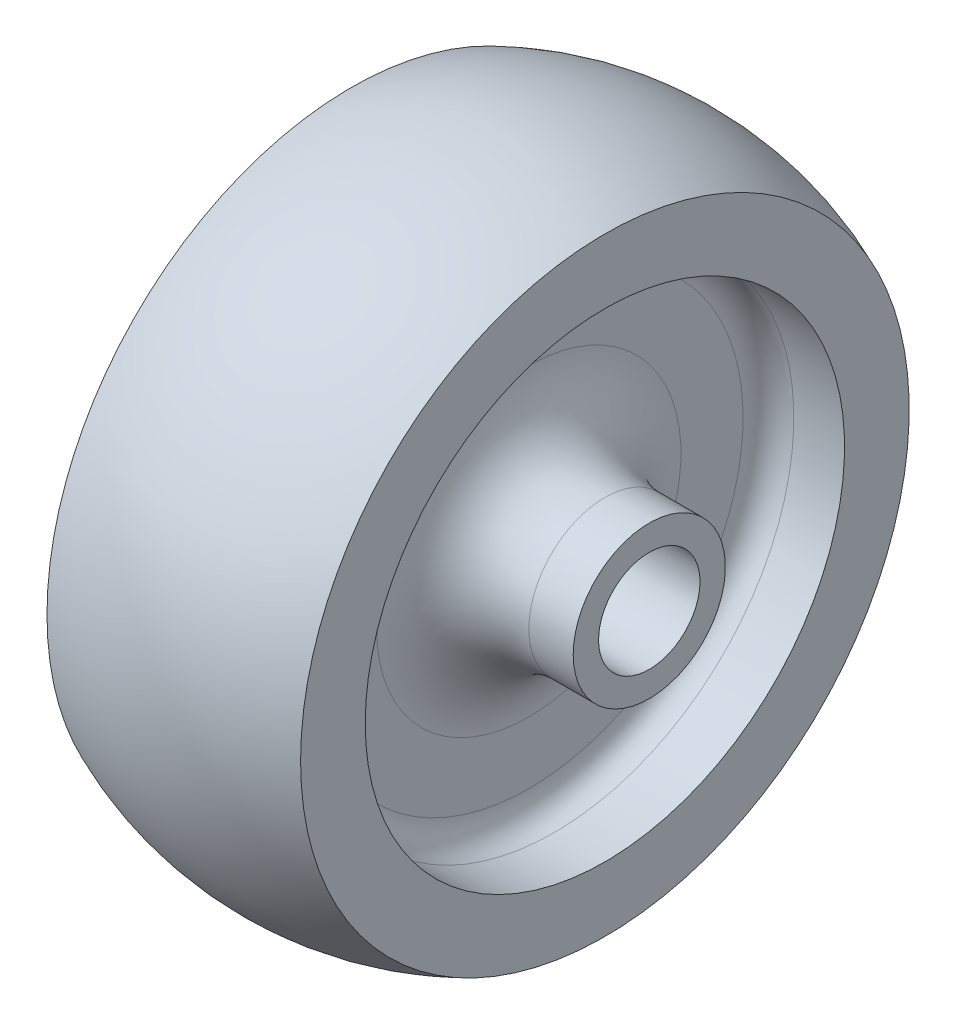
SolidWorks part; units mm, degrees
ref_plane "Front Plane" through (0, 0, 0) normal (0, 0, 1) x (1, 0, 0)
ref_plane "Top Plane" through (0, 0, 0) normal (0, 1, 0) x (1, 0, 0)
ref_plane "Right Plane" through (0, 0, 0) normal (1, 0, 0) x (0, 0, -1)
sketch "Sketch1" plane through (0, 0, 0) normal (0, 0, 1) x (1, 0, 0)
  line L0 (0, 0) -> (21.0336, 0) construction
  line L1 (0, 4) -> (0, 6)
  line L4 (0, 4) -> (27, 4)
  line L6 (0, 6) -> (3.5, 6)
  line L7 (3.5, 18.9) -> (3.5, 24)
  line L8 (23.5, 24) -> (23.5, 18.9)
  line L9 (23.5, 6) -> (27, 6)
  line L10 (27, 6) -> (27, 4)
  line L12 (3.5, 6) -> (9.5, 6)
  line L14 (3.5, 18.9) -> (7.5, 18.9)
  line L15 (9.5, 6) -> (9.5, 16.9)
  line L16 (23.5, 6) -> (17.5, 6)
  line L18 (23.5, 18.9) -> (19.5, 18.9)
  line L19 (17.5, 6) -> (17.5, 16.9)
  arc A0 (3.5, 24) -> (23.5, 24) centre (13.5, 1.0871) cw
  arc A1 (19.5, 18.9) -> (17.5, 16.9) centre (19.5, 16.9) ccw
  arc A2 (7.5, 18.9) -> (9.5, 16.9) centre (7.5, 16.9) cw
  point P20 (17.5, 18.9)
  point P23 (9.5, 18.9)
  dimension "D11" = 25
  dimension "D12" = 2
  dimension "D1" = 8
  dimension "D2" = 27
  dimension "D3" = 20
  dimension "D4" = 3.5
  dimension "D5" = 12
  dimension "D6" = 12
  dimension "D7" = 6
  dimension "D8" = 6
  dimension "D9" = 37.8
  dimension "D10" = 37.8
  dimension "D13" = 48
  dimension "D14" = 48
revolve "Revolve1" add sketch "Sketch1" angle 360 about L0
fillet "Fillet1" radius 6 2 edges at (17.5, 0, 6) (9.5, 0, 6)
